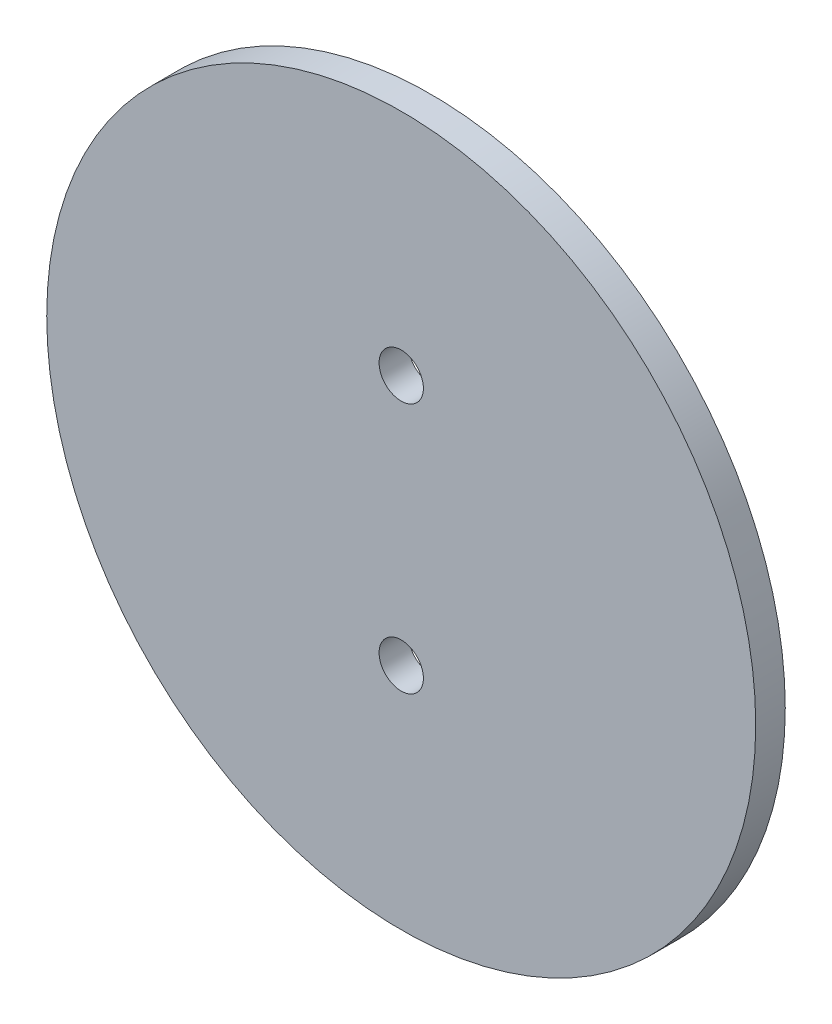
SolidWorks part; units mm, degrees
ref_plane "Front Plane" through (0, 0, 0) normal (0, 0, 1) x (1, 0, 0)
ref_plane "Top Plane" through (0, 0, 0) normal (0, 1, 0) x (1, 0, 0)
ref_plane "Right Plane" through (0, 0, 0) normal (1, 0, 0) x (0, 0, -1)
sketch "Sketch1" plane through (0, 0, 0) normal (0, 0, 1) x (1, 0, 0)
  line L0 (0, 26.9875) -> (0, -26.9875) construction
  circle A0 centre (0, 0) radius 76.2
  circle A1 centre (0, 26.9875) radius 4.7625
  circle A2 centre (0, -26.9875) radius 4.7625
  dimension "D1" = 152.4
  dimension "D2" = 53.975
extrude "Boss-Extrude1" add sketch "Sketch1" along normal blind 6.35
